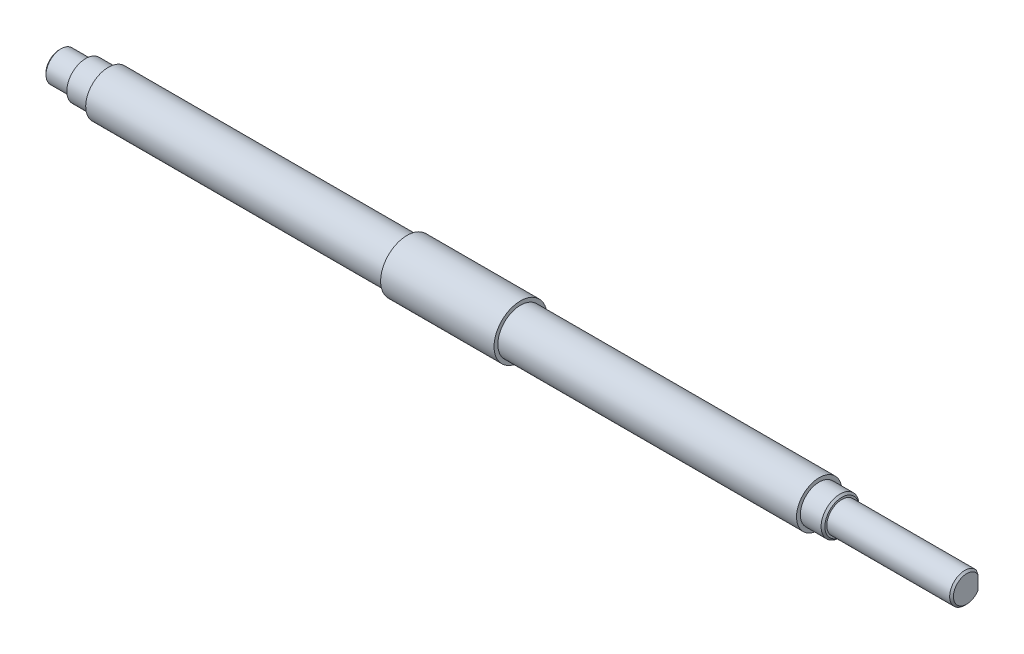
SolidWorks part; units mm, degrees
material "304"
ref_plane "前视基准面" through (0, 0, 0) normal (0, 0, 1) x (1, 0, 0)
ref_plane "上视基准面" through (0, 0, 0) normal (0, 1, 0) x (1, 0, 0)
ref_plane "右视基准面" through (0, 0, 0) normal (1, 0, 0) x (0, 0, -1)
sketch "草图1" plane through (0, 0, 0) normal (0, 0, 1) x (1, 0, 0)
  line L0 (-177.8106, 0) -> (177.8106, 0) construction
  line L1 (-107, 0) -> (-107, 4)
  line L2 (-107, 4) -> (-100, 4)
  line L3 (-94, 5) -> (-94, 6)
  line L4 (-94, 6) -> (-15, 6)
  line L5 (-15, 6) -> (-15, 7)
  line L6 (-15, 7) -> (15, 7)
  line L7 (15, 7) -> (15, 6)
  line L8 (15, 6) -> (94, 6)
  line L9 (94, 6) -> (94, 5)
  line L10 (94, 5) -> (100, 5)
  line L11 (100, 5) -> (100, 4)
  line L12 (100, 4) -> (133, 4)
  line L13 (133, 4) -> (133, 0)
  line L14 (0, 0) -> (0, 14) construction
  line L15 (-107, 0) -> (133, 0)
  line L16 (-94, 5) -> (-100, 5)
  line L17 (-100, 5) -> (-100, 4)
  point P19 (0, 7)
  dimension "D1" = 12
  dimension "D2" = 79
  dimension "D3" = 10
  dimension "D4" = 79
  dimension "D5" = 30
  dimension "D6" = 6
  dimension "D7" = 10
  dimension "D8" = 8
  dimension "D9" = 8
  dimension "D10" = 240
  dimension "D11" = 7
  dimension "D12" = 14
  dimension "D13" = 6
revolve "旋转1" add sketch "草图1" angle 360 about L15
ref_plane "基准面1" through (0, 0, -3) normal (0, 0, 1) x (1, 0, 0)
sketch "草图2" plane through (0, 0, -3) normal (0, 0, 1) x (1, 0, 0)
  line L0 (133, -4) -> (133, 4) construction
  line L1 (113, -9.4397) -> (138.5457, -9.4397)
  line L2 (113, -9.4397) -> (113, 9.2195)
  line L3 (113, 9.2195) -> (138.5457, 9.2195)
  line L4 (138.5457, -9.4397) -> (138.5457, 9.2195)
  dimension "D1" = 20
extrude "切除-拉伸1" cut sketch "草图2" against normal blind 10
chamfer "倒角1" distance 0.5 angle 45 3 edges at (133, 0, 4) (100, -5, 0) (-107, -4, 0)
